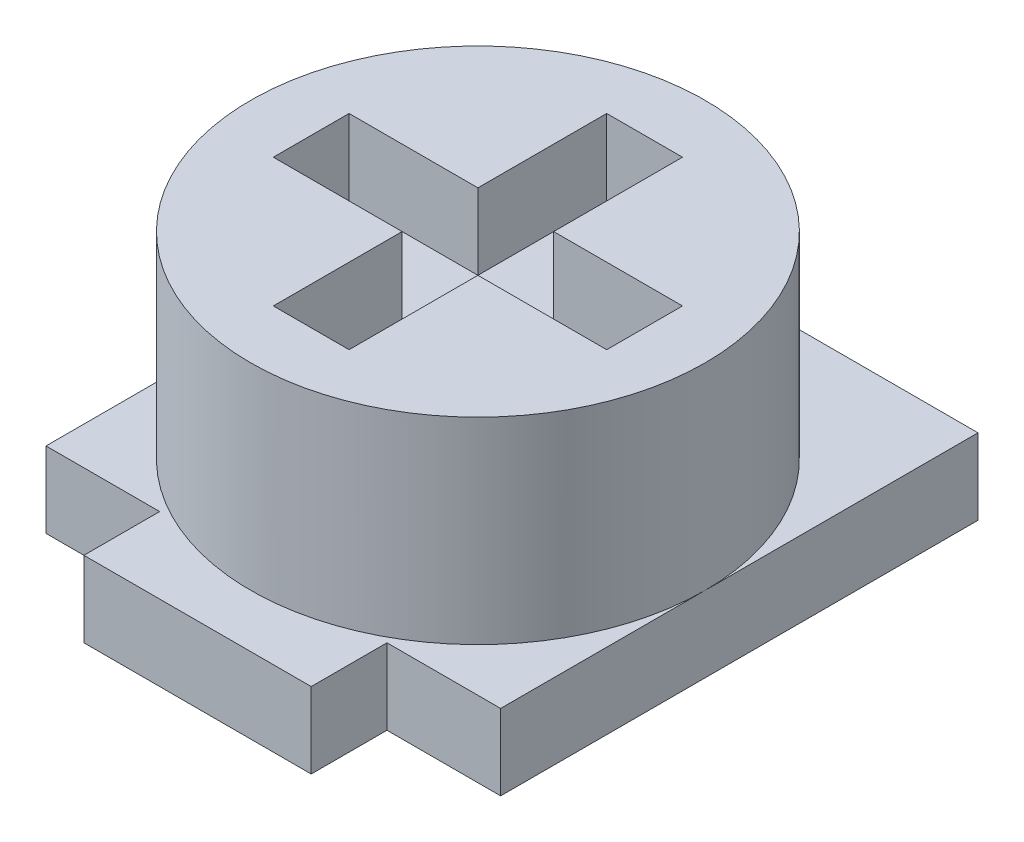
SolidWorks part; units mm, degrees
ref_plane "Front Plane" through (0, 0, 0) normal (0, 0, 1) x (1, 0, 0)
ref_plane "Top Plane" through (0, 0, 0) normal (0, 1, 0) x (1, 0, 0)
ref_plane "Right Plane" through (0, 0, 0) normal (1, 0, 0) x (0, 0, -1)
sketch "Sketch1" plane through (0, 0, 0) normal (0, 1, 0) x (1, 0, 0)
  circle A0 centre (0, 0) radius 1.5
  dimension "D1" = 3
extrude "Boss-Extrude1" add sketch "Sketch1" along normal blind 1.8
sketch "Sketch2" plane through (0, 0, 0) normal (0, -1, 0) x (1, 0, 0)
  line L0 (1.5, 1.35) -> (1.5, -1.8)
  line L5 (1.5, -1.8) -> (-1.5, -1.8)
  line L6 (-1.5, -1.8) -> (-1.5, 1.35)
  line L7 (-1.5, 1.35) -> (-0.75, 1.35)
  line L8 (-0.75, 1.35) -> (-0.75, 1.85)
  line L9 (-0.75, 1.85) -> (0.75, 1.85)
  line L10 (0.75, 1.85) -> (0.75, 1.35)
  line L11 (0.75, 1.35) -> (1.5, 1.35)
  point P7 (0, -1.8)
  point P10 (0.5492, 1.5)
  point P12 (0.6189, 1.5)
  point P13 (0.75, 1.451)
  dimension "D1" = 3
  dimension "D2" = 3.65
  dimension "D3" = 1.85
  dimension "D4" = 1.5
  dimension "D5" = 0.5
extrude "Boss-Extrude2" add sketch "Sketch2" against normal blind 0.5
sketch "Sketch4" plane through (0, 1.8, 0) normal (0, 1, 0) x (1, 0, 0)
  line L1 (0.25, 1.1) -> (-0.25, 1.1)
  line L2 (0.25, 1.1) -> (0.25, -1.1)
  line L3 (0.25, -1.1) -> (-0.25, -1.1)
  line L4 (-0.25, 1.1) -> (-0.25, -1.1)
  line L5 (0.25, 1.1) -> (-0.25, -1.1) construction
  line L6 (0.25, -1.1) -> (-0.25, 1.1) construction
  line L7 (-1.1, 0.25) -> (1.1, 0.25)
  line L8 (-1.1, 0.25) -> (-1.1, -0.25)
  line L9 (-1.1, -0.25) -> (1.1, -0.25)
  line L10 (1.1, 0.25) -> (1.1, -0.25)
  line L11 (-1.1, 0.25) -> (1.1, -0.25) construction
  line L12 (-1.1, -0.25) -> (1.1, 0.25) construction
  point P0 (0, 0)
  point P6 (0, 0)
  dimension "D1" = 0.5
  dimension "D2" = 2.2
extrude "Cut-Extrude1" cut sketch "Sketch4" against normal blind 0.5 contours L10 L7 L2 L9 | L4 L9 L2 L7 | L9 L4 L3 L2 | L8 L9 L4 L7 | L4 L7 L2 L1
